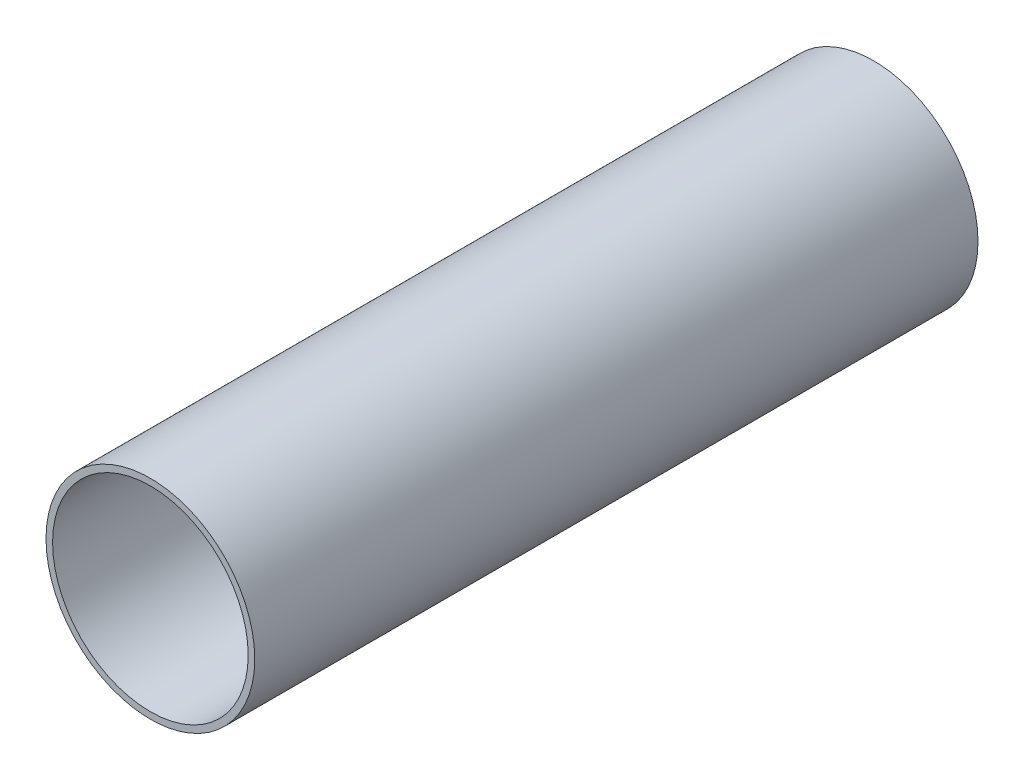
SolidWorks part; units mm, degrees
ref_plane "Front Plane" through (0, 0, 0) normal (0, 0, 1) x (1, 0, 0)
ref_plane "Top Plane" through (0, 0, 0) normal (0, 1, 0) x (1, 0, 0)
ref_plane "Right Plane" through (0, 0, 0) normal (1, 0, 0) x (0, 0, -1)
sketch "Sketch1" plane through (0, 0, 0) normal (0, 0, 1) x (1, 0, 0)
  circle A0 centre (0, 0) radius 31.75
  circle A1 centre (0, 0) radius 29.75
  point P4 (0, 0)
  point P5 (0, 0)
  dimension "D1" = 63.5
  dimension "D2" = 59.5
extrude "Boss-Extrude1" add sketch "Sketch1" along normal blind 220
